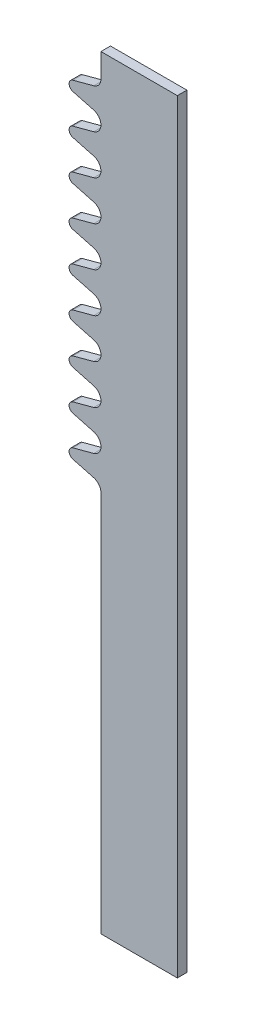
SolidWorks part; units mm, degrees
ref_plane "Front Plane" through (0, 0, 0) normal (0, 0, 1) x (1, 0, 0)
ref_plane "Top Plane" through (0, 0, 0) normal (0, 1, 0) x (1, 0, 0)
ref_plane "Right Plane" through (0, 0, 0) normal (1, 0, 0) x (0, 0, -1)
sketch "Sketch1" plane through (0, 0, 0) normal (0, 0, 1) x (1, 0, 0)
  line L1 (-1.7, -12) -> (1.7, -12)
  line L2 (-1.7, -12) -> (-1.7, 12)
  line L3 (-1.7, 12) -> (1.7, 12)
  line L4 (1.7, -12) -> (1.7, 12)
  line L5 (-1.7, -12) -> (1.7, 12) construction
  line L6 (-1.7, 12) -> (1.7, -12) construction
  point P0 (0, 0)
  dimension "D1" = 3.4
  dimension "D2" = 24
extrude "Boss-Extrude1" add sketch "Sketch1" against normal blind 0.3
sketch "Sketch2" plane through (0, 0, 0) normal (0, 0, 1) x (1, 0, 0)
  line L0 (-0.7, -12) -> (-0.7, 0)
  line L1 (-1.7, -12) -> (1.7, -12) construction
  line L2 (-1.7, 0.625) -> (-0.2197, 0.625) construction
  line L3 (-1.7, 12) -> (-1.7, -12) construction
  line L4 (-1.5814, 0.4705) -> (-0.9263, 0.2949)
  line L6 (-1.0053, 0) -> (-1.9098, 0) construction
  line L11 (-1.7, 0.625) -> (-2.2, 0.625)
  line L12 (-0.7, -12) -> (-2.2, -12)
  line L13 (-2.2, 12) -> (-2.2, -12)
  line L14 (-2.2, 0.625) -> (-2.2, -12)
  arc A0 (-1.5814, 0.4705) -> (-1.7, 0.625) centre (-1.54, 0.625) cw
  arc A1 (-0.7, 0) -> (-0.9263, 0.2949) centre (-1.0053, 0) ccw
  point P14 (-0.7, 0.2343)
  line M16 (-1.7, 12) -> (-1.7, -12)
  line M17 (-1.7, -12) -> (1.7, -12)
  dimension "D2" = 0.16
  dimension "D3" = 15
  dimension "D1" = 1
  dimension "D4" = 0.625
  dimension "D5" = 12
  dimension "D8" = 0.5
extrude "Cut-Extrude1" cut sketch "Sketch2" against normal through all contours L0 A1 L4 A0 M16 M17
sketch "Sketch3" plane through (0, 0, 0) normal (0, 0, 1) x (1, 0, 0)
  line L0 (-1.7, 1.25) -> (-1.0053, 1.25) construction
  line L1 (-1.7, 12) -> (-1.7, 0.625) construction
  line L2 (-0.7, 0) -> (-0.7, 2.0531) construction
  line L3 (-1.5814, 0.7795) -> (-0.9263, 0.9551)
  line L5 (-1.7, 1.875) -> (-1.7, 0.625)
  line L6 (-1.5814, 1.7205) -> (-0.9263, 1.5449)
  arc A0 (-0.9263, 0.9551) -> (-0.9263, 1.5449) centre (-1.0053, 1.25) ccw
  arc A1 (-0.7, 0) -> (-0.9263, 0.2949) centre (-1.0053, 0) ccw construction
  arc A2 (-1.5814, 0.7795) -> (-1.7, 0.625) centre (-1.54, 0.625) ccw
  arc A3 (-1.7, 0.625) -> (-1.5814, 0.4705) centre (-1.54, 0.625) ccw construction
  arc A4 (-1.5814, 1.7205) -> (-1.7, 1.875) centre (-1.54, 1.875) cw
  dimension "D1" = 1.25
  dimension "D2" = 15
extrude "Cut-Extrude2" cut sketch "Sketch3" against normal through all
pattern_linear "LPattern1" count 9 spacing 1.25 along (0, 1, 0) of "Cut-Extrude2"
sketch "Sketch4" plane through (0, 0, 0) normal (0, 0, 1) x (1, 0, 0)
  line L0 (-0.7, 11.25) -> (-0.7, 12)
  line L1 (1.7, 12) -> (-1.7, 12) construction
  line L3 (-1.7, 12) -> (-1.7, 11.875) construction
  line L4 (-0.9263, 11.5449) -> (-1.5814, 11.7205) construction
  line L5 (-1.7, 12) -> (-1.7, 11.875)
  line L6 (-0.9263, 11.5449) -> (-1.5814, 11.7205)
  line L7 (-0.7, 12) -> (-1.7, 12)
  arc A0 (-0.9263, 10.9551) -> (-0.9263, 11.5449) centre (-1.0053, 11.25) ccw construction
  arc A1 (-1.7, 11.875) -> (-1.5814, 11.7205) centre (-1.54, 11.875) ccw construction
  arc A2 (-1.7, 11.875) -> (-1.5814, 11.7205) centre (-1.54, 11.875) ccw
  arc A3 (-0.7, 11.25) -> (-0.9263, 11.5449) centre (-1.0053, 11.25) ccw
extrude "Cut-Extrude4" cut sketch "Sketch4" against normal through all
